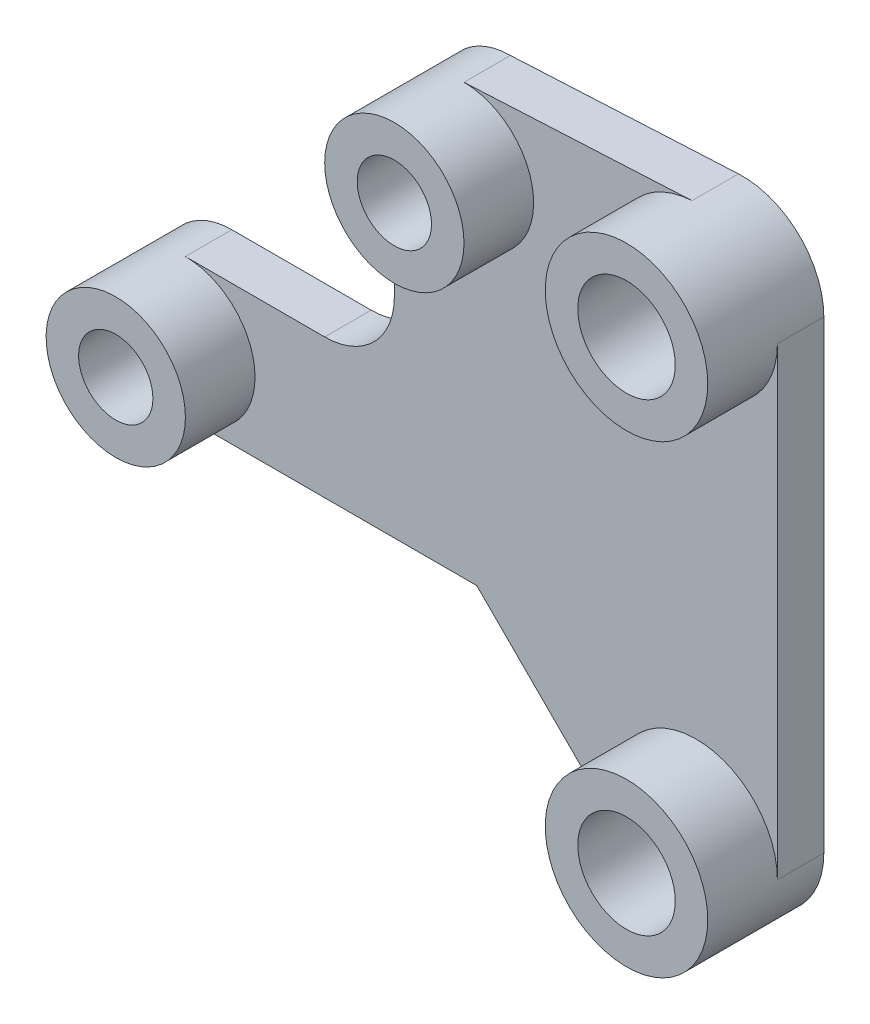
SolidWorks part; units mm, degrees
ref_plane "Front Plane" through (0, 0, 0) normal (0, 0, 1) x (1, 0, 0)
ref_plane "Top Plane" through (0, 0, 0) normal (0, 1, 0) x (1, 0, 0)
ref_plane "Right Plane" through (0, 0, 0) normal (1, 0, 0) x (0, 0, -1)
sketch "Sketch1" plane through (0, 0, 0) normal (0, 0, 1) x (1, 0, 0)
  line L0 (0, 0) -> (15.0744, 0) construction
  line L1 (15.0744, 0) -> (15.0744, 12.5) construction
  line L2 (15.0744, 12.5) -> (-2.9216, 12.5) construction
  line L3 (28.6937, -5.2838) -> (15.0744, -5.2838) construction
  line L4 (15.0744, -5.2838) -> (15.0744, 0) construction
  line L5 (22, -7.5) -> (22, 12.5) construction
  line L6 (0, 3) -> (6, 3)
  line L7 (9, 6) -> (9, 12.5)
  line L8 (12, 15.5) -> (21.8237, 15.9956)
  line L9 (25.5, 12.5) -> (25.5, -7.5)
  line L10 (0, -3) -> (12.5503, -3)
  line L11 (12.5503, -3) -> (19.5251, -9.9749)
  line L12 (15.0744, 12.5) -> (38.4849, 12.5) construction
  arc A0 (0, 3) -> (0, -3) centre (0, 0) ccw
  arc A1 (12, 15.5) -> (9, 12.5) centre (12, 12.5) ccw
  arc A4 (6, 3) -> (9, 6) centre (6, 6) ccw
  arc A5 (25.5, 12.5) -> (21.8237, 15.9956) centre (22, 12.5) ccw
  arc A6 (19.5251, -9.9749) -> (25.5, -7.5) centre (22, -7.5) ccw
  point P1 (14.1252, -3)
  point P7 (25, 10.5)
  point P8 (25, 11)
  point P26 (25, 14.5)
  point P32 (25.0827, -9.0078)
  point P33 (27.9447, 11)
  point P34 (28.5, 11)
  point P35 (28.5827, 10.9922)
  dimension "D1" = 6
  dimension "D2" = 6
  dimension "D3" = 20
  dimension "D10" = 3
  dimension "D11" = 7
  dimension "D5" = 12.5
  dimension "D6" = 10
  dimension "D7" = 12
  dimension "D9" = 135
extrude "Boss-Extrude1" add sketch "Sketch1" along normal blind 2
sketch "Sketch2" plane through (0, 0, 2) normal (0, 0, 1) x (1, 0, 0)
  circle A0 centre (0, 0) radius 3
  circle A3 centre (12, 12.5) radius 3
  circle A4 centre (22, 12.5) radius 3.5
  circle A5 centre (22, -7.5) radius 3.5
  arc A6 (12, 15.5) -> (9, 12.5) centre (12, 12.5) ccw construction
  point P3 (15, 10)
  point P7 (0, 0)
  point P17 (25, 10)
  point P18 (25, 10)
  point P19 (25.2591, 11)
  point P20 (25, 11)
  point P21 (25.0827, 10.9922)
  point P23 (0, 0)
  point P24 (25.0827, -9.0078)
  point P26 (0, 0)
  point P27 (0, 0)
  point P28 (22, 9)
  point P30 (22, -11)
  dimension "D1" = 6
  dimension "D2" = 6
  dimension "D3" = 7
extrude "Boss-Extrude2" add sketch "Sketch2" along normal blind 3
sketch "Sketch3" plane through (0, 0, 5) normal (0, 0, 1) x (1, 0, 0)
  circle A0 centre (0, 0) radius 1.6
  circle A1 centre (12, 12.5) radius 1.6
  circle A2 centre (22, 12.5) radius 2.1
  circle A3 centre (22, -7.5) radius 2.1
  point P12 (25, 10)
  point P13 (25.0827, 10.9922)
  point P15 (0, 0)
  point P16 (25.0827, -9.0078)
  point P18 (0, 0)
  point P19 (0, 0)
  point P20 (22, 9)
  point P22 (22, -11)
  dimension "D1" = 3.2
  dimension "D2" = 3.2
  dimension "D3" = 4.2
extrude "Cut-Extrude1" cut sketch "Sketch3" against normal through all
